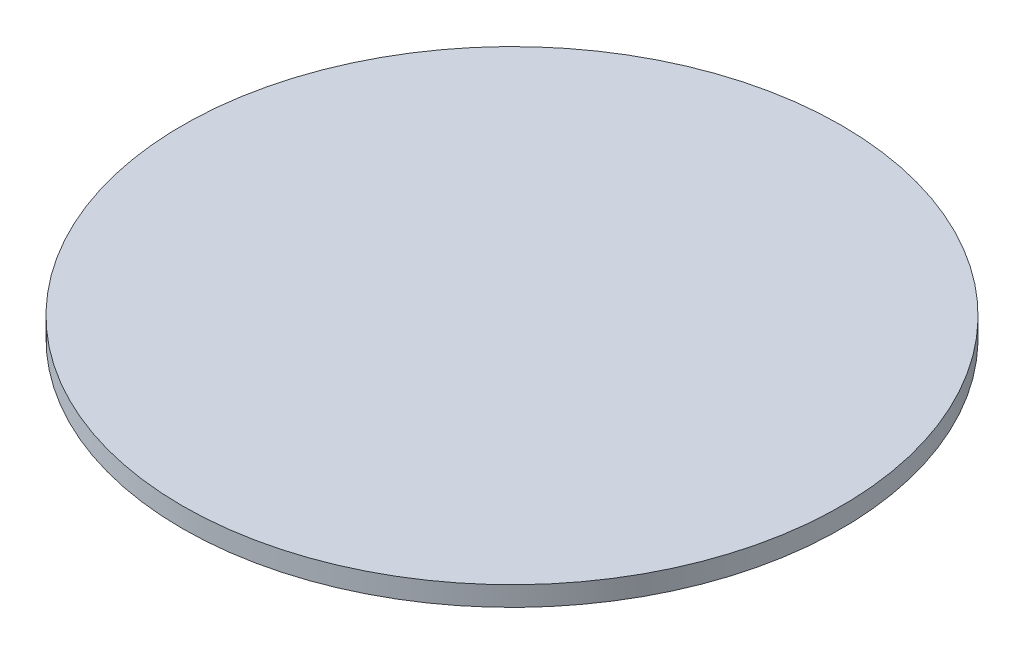
SolidWorks part; units mm, degrees
ref_plane "前视基准面" through (0, 0, 0) normal (0, 0, 1) x (1, 0, 0)
ref_plane "上视基准面" through (0, 0, 0) normal (0, 1, 0) x (1, 0, 0)
ref_plane "右视基准面" through (0, 0, 0) normal (1, 0, 0) x (0, 0, -1)
other "Configuration Table"
sketch "Sketch1" plane through (0, 0, 0) normal (0, 1, 0) x (1, 0, 0)
  circle A0 centre (0, 0) radius 33.51
  dimension "D1" = 67.02
extrude "Boss-Extrude1" add sketch "Sketch1" along normal blind 2
